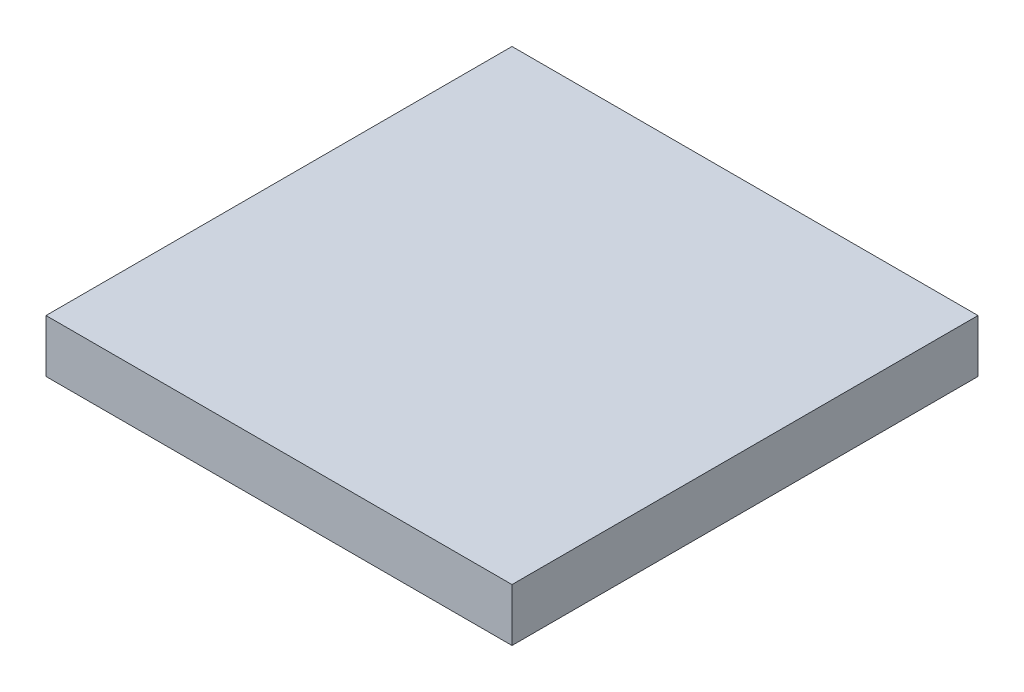
SolidWorks part; units mm, degrees
ref_plane "Front Plane" through (0, 0, 0) normal (0, 0, 1) x (1, 0, 0)
ref_plane "Top Plane" through (0, 0, 0) normal (0, 1, 0) x (1, 0, 0)
ref_plane "Right Plane" through (0, 0, 0) normal (1, 0, 0) x (0, 0, -1)
sketch "Sketch1" plane through (0, 0, 0) normal (0, 1, 0) x (1, 0, 0)
  line L1 (-0.6913, 0.7109) -> (0.8087, 0.7109)
  line L2 (-0.6913, 0.7109) -> (-0.6913, -0.7891)
  line L3 (-0.6913, -0.7891) -> (0.8087, -0.7891)
  line L4 (0.8087, 0.7109) -> (0.8087, -0.7891)
  dimension "D1" = 1.5
  dimension "D2" = 1.5
extrude "Boss-Extrude1" add sketch "Sketch1" along normal blind 0.17
